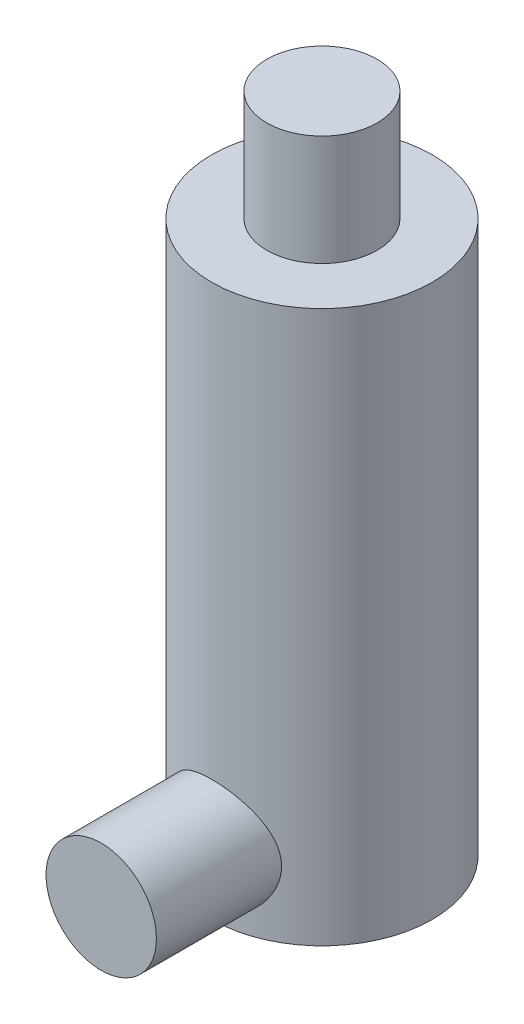
SolidWorks part; units mm, degrees
ref_plane "Front Plane" through (0, 0, 0) normal (0, 0, 1) x (1, 0, 0)
ref_plane "Top Plane" through (0, 0, 0) normal (0, 1, 0) x (1, 0, 0)
ref_plane "Right Plane" through (0, 0, 0) normal (1, 0, 0) x (0, 0, -1)
sketch "Sketch1" plane through (0, 0, 0) normal (0, 1, 0) x (1, 0, 0)
  circle A0 centre (0, 0) radius 5
  dimension "D1" = 10
extrude "Boss-Extrude1" add sketch "Sketch1" along normal blind 25
ref_plane "Plane1" through (0, 0, 5) normal (0, 0, 1) x (1, 0, 0)
sketch "Sketch2" plane through (0, 0, 5) normal (0, 0, 1) x (1, 0, 0)
  circle A0 centre (0, 3) radius 2.5
  point P2 (0, 0)
  point P8 (0, 0)
  point P9 (0, 25.9624)
  dimension "D1" = 5
  dimension "D2" = 3
extrude "Boss-Extrude2" add sketch "Sketch2" along normal blind 5 and the other way up to surface separate body
sketch "Sketch4" plane through (0, 25, 0) normal (0, 1, 0) x (1, 0, 0)
  circle A0 centre (0, 0) radius 2.5
  dimension "D1" = 5
extrude "Boss-Extrude3" add sketch "Sketch4" along normal blind 5
